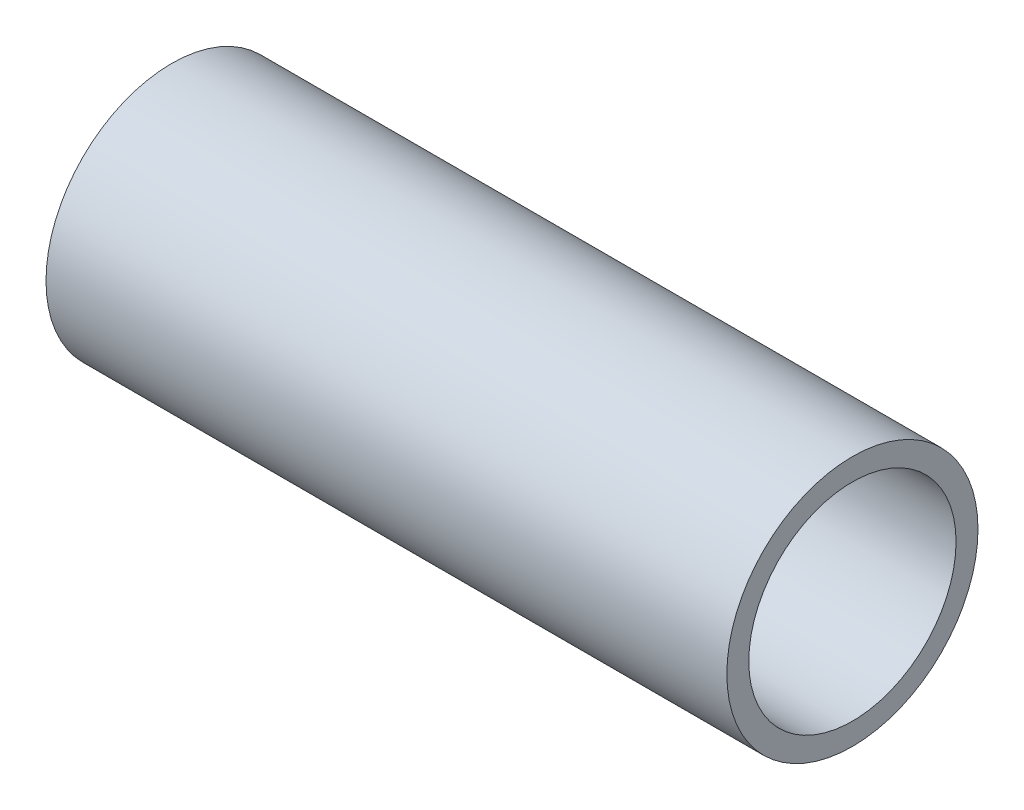
SolidWorks part; units mm, degrees
ref_plane "Front Plane" through (0, 0, 0) normal (0, 0, 1) x (1, 0, 0)
ref_plane "Top Plane" through (0, 0, 0) normal (0, 1, 0) x (1, 0, 0)
ref_plane "Right Plane" through (0, 0, 0) normal (1, 0, 0) x (0, 0, -1)
sketch "Sketch1" plane through (0, 0, 0) normal (0, 0, 1) x (1, 0, 0)
  line L0 (-25.0028, 0) -> (91.6769, 0) construction
  line L1 (0, 21.082) -> (0, 17.399)
  line L2 (0, 17.399) -> (114.3, 17.399)
  line L3 (114.3, 17.399) -> (114.3, 21.082)
  line L4 (114.3, 21.082) -> (0, 21.082)
  line L5 (0, 33.7623) -> (0, -23.1766) construction
  dimension "D1" = 34.798
  dimension "D2" = 42.164
  dimension "D3" = 114.3
revolve "Revolve1" add sketch "Sketch1" angle 360 about L0
